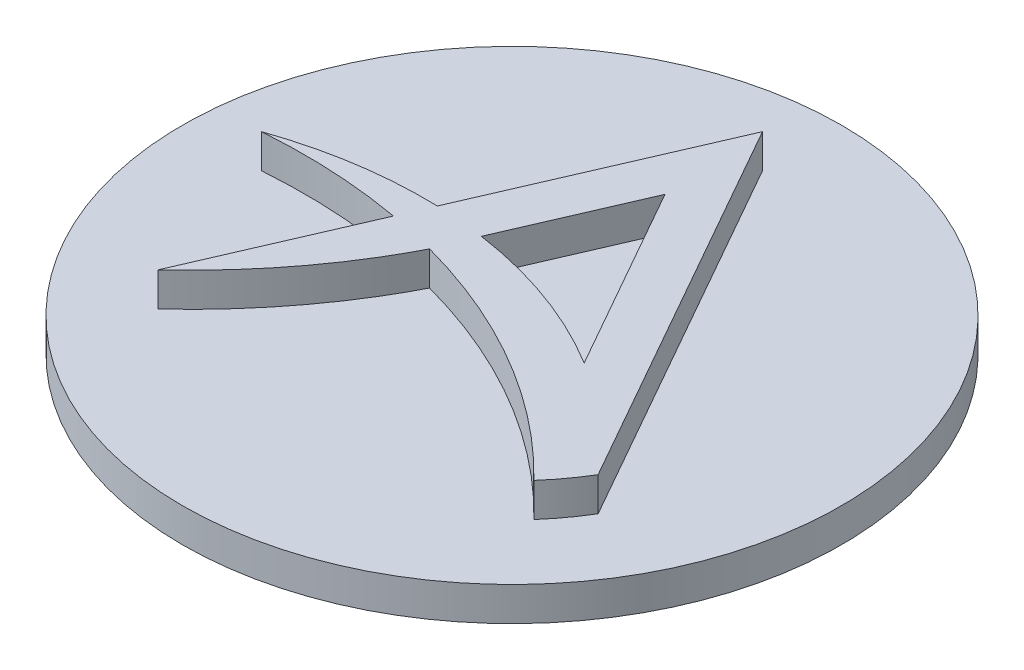
SolidWorks part; units mm, degrees
material "Alloy Steel"
ref_plane "Front Plane" through (0, 0, 0) normal (0, 0, 1) x (1, 0, 0)
ref_plane "Top Plane" through (0, 0, 0) normal (0, 1, 0) x (1, 0, 0)
ref_plane "Right Plane" through (0, 0, 0) normal (1, 0, 0) x (0, 0, -1)
sketch "Sketch1" plane through (0, 0, 0) normal (0, 1, 0) x (1, 0, 0)
  circle A0 centre (0, 0) radius 24.3
  dimension "D1" = 48.6
extrude "Boss-Extrude1" add sketch "Sketch1" along normal blind 2.5
sketch "Sketch2" plane through (0, 2.5, 0) normal (0, 1, 0) x (1, 0, 0)
  line L0 (-13.4613, -12.6447) -> (-8.2171, -0.5236)
  line L1 (0, 18.4687) -> (15.8425, -9.4927)
  line L2 (-3.681, 1.4234) -> (-0.631, 8.4731)
  line L3 (7.1444, 5.872) -> (15.8654, -9.5202)
  line L4 (8.1987, -2.8785) -> (2.4615, 7.2474)
  line L5 (-0.631, 8.4731) -> (0.4073, 10.8729)
  line L6 (2.4615, 7.2474) -> (0.4073, 10.8729)
  line L7 (-7.2407, 1.7331) -> (0, 18.4687)
  arc A1 (-18.4687, 0) -> (-7.2407, 1.7331) centre (-8.1654, -29.5139) cw
  arc A2 (-18.4687, 0) -> (-8.2171, -0.5236) centre (-15.409, -40.7165) cw
  circle A3 centre (0, 0) radius 24.3
  arc A4 (-3.681, 1.4234) -> (8.1987, -2.8785) centre (-8.1654, -29.5139) cw
  arc A5 (-4.7864, -1.2912) -> (13.8412, -12.2276) centre (-15.409, -40.7165) cw
  arc A6 (13.8412, -12.2276) -> (15.8462, -9.4864) centre (0, 0) ccw
  spline S0 degree 2 poles (-13.4613, -12.6447) (-8.0279, -7.6031) (-4.7864, -1.2912) knots 0 0 0 0.698779 0.698779 0.698779
  dimension "D1" = 3.39
  dimension "D2" = 3.39
extrude "Boss-Extrude3" add sketch "Sketch2" along normal blind 2.5 contours L0 S0 A5 A6 L1 L7 A1 A2 A4 L2 L5 L6 L4
